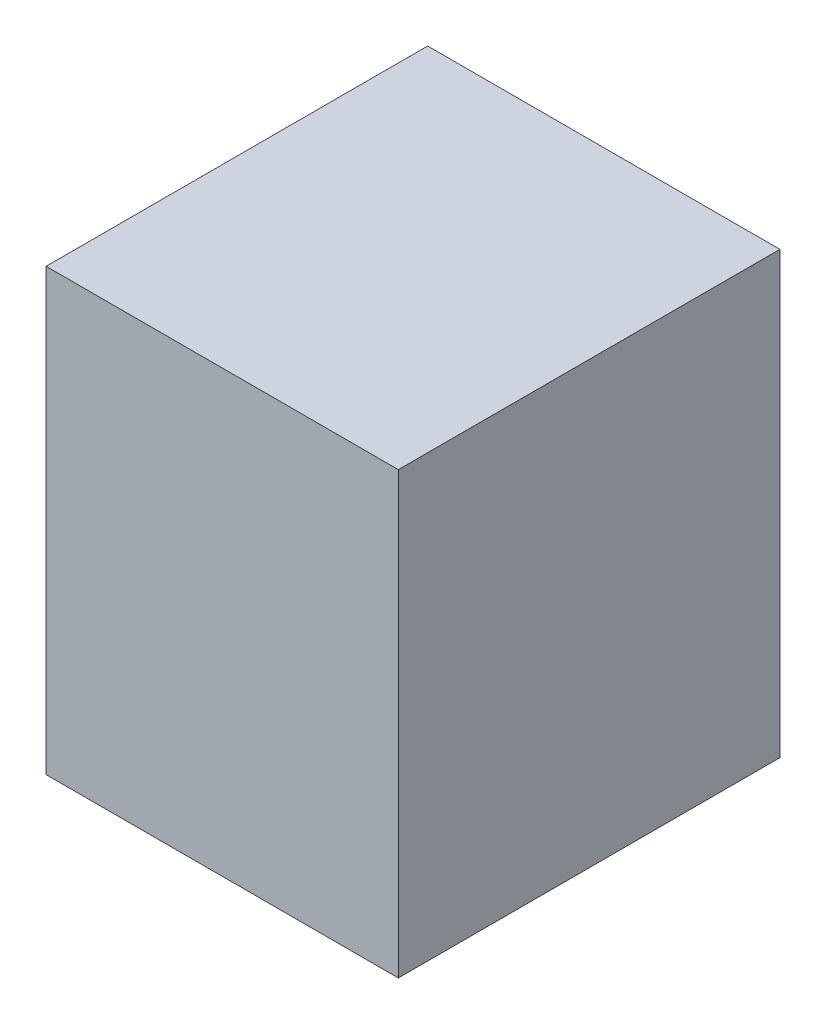
SolidWorks part; units mm, degrees
material "ABS"
ref_plane "Front Plane" through (0, 0, 0) normal (0, 0, 1) x (1, 0, 0)
ref_plane "Top Plane" through (0, 0, 0) normal (0, 1, 0) x (1, 0, 0)
ref_plane "Right Plane" through (0, 0, 0) normal (1, 0, 0) x (0, 0, -1)
sketch "Sketch1" plane through (0, 0, 0) normal (0, 0, 1) x (1, 0, 0)
  line L1 (-6, 7.5) -> (6, 7.5)
  line L2 (-6, 7.5) -> (-6, -7.5)
  line L3 (-6, -7.5) -> (6, -7.5)
  line L4 (6, 7.5) -> (6, -7.5)
  line L5 (-6, 7.5) -> (6, -7.5) construction
  line L6 (-6, -7.5) -> (6, 7.5) construction
  point P0 (0, 0)
  dimension "D1" = 12
  dimension "D2" = 15
extrude "Boss-Extrude1" add sketch "Sketch1" along normal blind 13
sketch "Sketch2" plane through (0, 0, 0) normal (0, 0, 1) x (1, 0, 0)
  line L0 (0, 6.435) -> (0, -7.5) construction
  line L1 (-6, -7.5) -> (6, -7.5) construction
  line L2 (1.3313, 6.435) -> (-1.3313, 6.435)
  line L3 (-1.3313, 6.435) -> (-1.3313, 5.674)
  line L4 (-1.3313, 5.674) -> (-2.9498, 5.674)
  line L5 (-2.9498, 5.674) -> (-2.9498, 4.1978)
  line L6 (-2.9498, 4.1978) -> (-5.0512, 4.1978)
  line L7 (-5.0512, 4.1978) -> (-5.0512, -7.5)
  line L8 (-5.0512, -7.5) -> (5.0512, -7.5)
  line L9 (5.0512, 4.1978) -> (5.0512, -7.5)
  line L10 (2.9498, 4.1978) -> (5.0512, 4.1978)
  line L11 (2.9498, 5.674) -> (2.9498, 4.1978)
  line L12 (1.3313, 5.674) -> (2.9498, 5.674)
  line L13 (1.3313, 6.435) -> (1.3313, 5.674)
extrude "Cut-Extrude1" cut sketch "Sketch2" along normal blind 8
